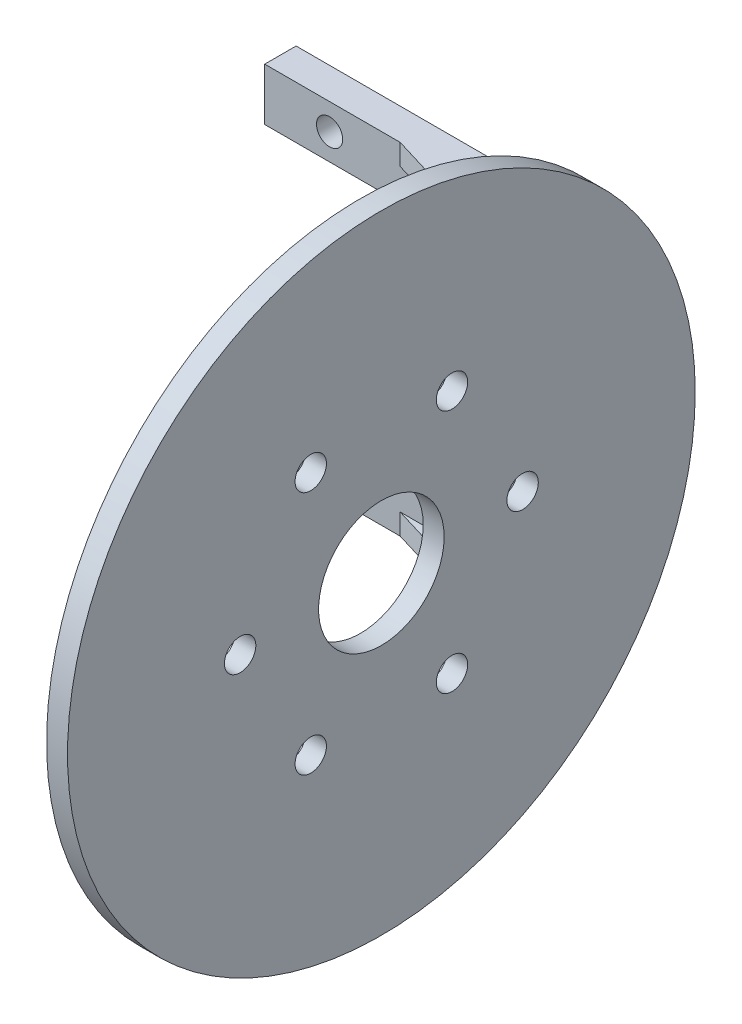
SolidWorks part; units mm, degrees
ref_plane "Front" through (0, 0, 0) normal (0, 0, 1) x (1, 0, 0)
ref_plane "Top" through (0, 0, 0) normal (0, 1, 0) x (1, 0, 0)
ref_plane "Right" through (0, 0, 0) normal (1, 0, 0) x (0, 0, -1)
sketch "Эскиз1" plane through (0, 0, 0) normal (0, 0, 1) x (1, 0, 0)
  line L0 (-10.0342, 0) -> (23.3567, 0) construction
  line L1 (0, 13.8) -> (0, -9.1553) construction
  line L3 (-6.2, 16.3) -> (11.2, 16.3)
  line L4 (-6.2, 16.3) -> (-6.2, 11.3)
  line L5 (-6.2, 11.3) -> (11.2, 11.3)
  line L6 (11.2, 16.3) -> (11.2, 11.3)
  line L7 (11.2, 16.3) -> (6.2, 16.3)
  line L8 (11.2, 16.3) -> (11.2, 0)
  line L9 (11.2, 0) -> (6.2, 0)
  line L10 (6.2, 16.3) -> (6.2, 0)
  circle A0 centre (0, 13.8) radius 1.25
  dimension "D2" = 6.2
  dimension "D7" = 2.5
  dimension "D1" = 2.5
  dimension "D3" = 12.4
  dimension "D4" = 5
  dimension "D5" = 5
  dimension "D6" = 11.3
extrude "Бобышка-Вытянуть1" add sketch "Эскиз1" along normal blind 3 contours L10 L3 L4 L5 A0 | L3 L10 L5 L6 | L5 L10 L9 L8
sketch "Эскиз2" plane through (11.2, 0, 0) normal (1, 0, 0) x (0, 0, -1)
  line L4 (0, 0) -> (0, 16.3)
  line L5 (0, 16.3) -> (-3, 16.3)
  line L6 (-3, 16.3) -> (-3, 0)
  line L7 (-3, 0) -> (0, 0)
  line L8 (0, 0) -> (0, 16.3)
  line L9 (0, 16.3) -> (-3, 16.3)
  line L10 (-3, 16.3) -> (-3, 0)
  line L11 (-3, 0) -> (0, 0)
  dimension "D1" = 0
extrude "Бобышка-Вытянуть2" add sketch "Эскиз2" along normal blind 12
sketch "Эскиз3" plane through (0, 16.3, 0) normal (0, 1, 0) x (1, 0, 0)
  line L0 (23.2, -3) -> (23.2, -8)
  line L1 (23.2, -8) -> (6.75, -3)
  line L2 (-1.25, -3) -> (1.25, -3) construction
  line L3 (-1.25, -3) -> (1.25, -3)
  line L4 (23.2, 0) -> (-6.2, 0)
  line L5 (-6.2, 0) -> (-6.2, -3)
  line L6 (-6.2, -3) -> (23.2, -3)
  line L7 (23.2, -3) -> (23.2, 0)
  line L8 (23.2, 0) -> (-6.2, 0)
  line L9 (-6.2, 0) -> (-6.2, -3)
  line L10 (-6.2, -3) -> (23.2, -3)
  line L11 (23.2, -3) -> (23.2, 0)
  line M8 (-6.2, -3) -> (23.2, -3)
  dimension "D2" = 5
  dimension "D3" = 5.5
  dimension "D1" = 0
extrude "Бобышка-Вытянуть3" add sketch "Эскиз3" against normal blind 2 contours L1 L0 M8
mirror "Зеркальное отражение1" about plane through (0, 0, 3) normal (0, -1, 0) of "Бобышка-Вытянуть2", "Бобышка-Вытянуть1", "Бобышка-Вытянуть3"
sketch "Эскиз4" plane through (23.2, 0, 0) normal (1, 0, 0) x (0, 0, -1)
  line L0 (6.75, 0) -> (-23.25, 0) construction
  line L1 (0, -16.3) -> (0, 16.3) construction
  line L2 (-23.25, -30) -> (-23.25, 30) construction
  line L3 (-23.25, 0) -> (-36.75, 0) construction
  circle A0 centre (-23.25, 0) radius 30
  circle A1 centre (-23.25, 0) radius 6
  circle A2 centre (-30, 11.6913) radius 1.5
  circle A3 centre (-16.5, -11.6913) radius 1.5
  circle A4 centre (-36.75, 0) radius 1.5
  circle A5 centre (-9.75, 0) radius 1.5
  circle A6 centre (-16.5, 11.6913) radius 1.5
  circle A7 centre (-30, -11.6913) radius 1.5
  circle A8 centre (-9.75, 0) radius 1.5
  circle A9 centre (-36.75, 0) radius 1.5
  circle A10 centre (-16.5, -11.6913) radius 1.5
  circle A11 centre (-30, 11.6913) radius 1.5
  circle A12 centre (-30, -11.6913) radius 1.5
  circle A13 centre (-16.5, 11.6913) radius 1.5
  point P35 (-23.25, 0)
  line M1 (-3, 14.3) -> (-3, -14.3)
  line M2 (-3, -14.3) -> (-8, -14.3)
  line M3 (-8, -14.3) -> (-8, -16.3)
  line M4 (-8, -16.3) -> (0, -16.3)
  line M5 (0, -16.3) -> (0, 16.3)
  line M6 (0, 16.3) -> (-8, 16.3)
  line M7 (-8, 16.3) -> (-8, 14.3)
  line M8 (-8, 14.3) -> (-3, 14.3)
  dimension "D1" = 60
  dimension "D3" = 12
  dimension "D4" = 3
  dimension "D2" = 23.25
  dimension "D5" = 6
  dimension "D6" = 27
extrude "Бобышка-Вытянуть4" add sketch "Эскиз4" along normal blind 2 contours A0 A7 A6 A5 A4 A3 A2 A1 M1 M8 M7 M6 M5 M4 M3 M2 | M8 M1 M2 M3 M4 M5 M6 M7
fillet "Скругление2" radius 2 7 edges at (23.2, -14.3, 5.5) (23.2, 14.3, 5.5) (23.2, 16.3, 4) (23.2, -16.3, 4) (23.2, -15.3, 8) (23.2, 15.3, 8) (23.2, 0, 3)
